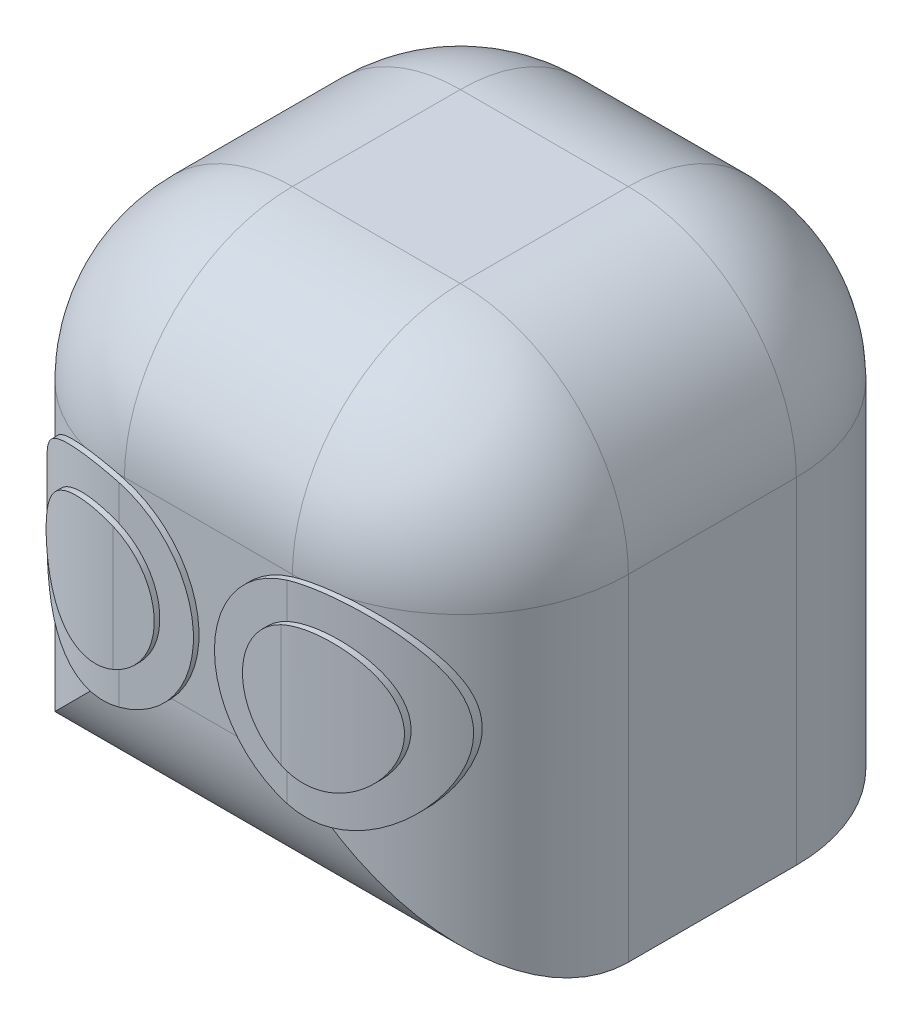
SolidWorks part; units mm, degrees
ref_plane "Alzado" through (0, 0, 0) normal (0, 0, 1) x (1, 0, 0)
ref_plane "Planta" through (0, 0, 0) normal (0, 1, 0) x (1, 0, 0)
ref_plane "Vista lateral" through (0, 0, 0) normal (1, 0, 0) x (0, 0, -1)
sketch "Croquis1" plane through (0, 0, 0) normal (0, 0, 1) x (1, 0, 0)
  line L1 (-56.7508, 42.2925) -> (33.2492, 42.2925)
  line L2 (-56.7508, 42.2925) -> (-56.7508, -47.7075)
  line L3 (-56.7508, -47.7075) -> (33.2492, -47.7075)
  line L4 (33.2492, 42.2925) -> (33.2492, -47.7075)
extrude "Saliente-Extruir1" add sketch "Croquis1" along normal blind 90
fillet "Redondeo2" radius 30 9 edges at (33.2492, 42.2925, 45) (-11.7508, 42.2925, 90) (-56.7508, 42.2925, 45) (-11.7508, 42.2925, 0) (-11.7508, -47.7075, 90) (-56.7508, -2.7075, 0) (33.2492, -2.7075, 0) (33.2492, -2.7075, 90) (-56.7508, -2.7075, 90)
sketch "Croquis2" plane through (0, 0, 90) normal (0, 0, 1) x (1, 0, 0)
  circle A0 centre (8.3242, -5.3588) radius 18
  circle A1 centre (-31.429, -5.3588) radius 18
extrude "Saliente-Extruir2" add sketch "Croquis2" along normal blind 1 and the other way blind 12
sketch "Croquis3" plane through (0, 42.2925, 0) normal (0, 1, 0) x (1, 0, 0)
  line L7 (-11.7508, -90) -> (-11.7508, -72.6432)
  line L8 (-26.7508, -91) -> (-50.1404, -91)
  line L9 (-50.1404, -91) -> (-50.1404, -80.3451)
  line L10 (3.2492, -90) -> (-26.7508, -90) construction
  line L11 (3.2492, -91) -> (26.6389, -91)
  line L12 (26.6389, -91) -> (26.6389, -80.3451)
  arc A1 (-50.1404, -80.3451) -> (-26.7508, -91) centre (-26.7508, -60) ccw
  arc A2 (26.6389, -80.3451) -> (3.2492, -91) centre (3.2492, -60) cw
extrude "Cortar-Extruir1" cut sketch "Croquis3" against normal blind 74 contours A1 L9 L8 | L12 A2 L11
sketch "Croquis4" plane through (0, 0, 91) normal (0, 0, 1) x (1, 0, 0)
  circle A0 centre (-31.429, -5.3588) radius 12
  circle A1 centre (8.3242, -5.3588) radius 12
extrude "Saliente-Extruir3" add sketch "Croquis4" against normal blind 6 and the other way blind 1
sketch "Croquis5" plane through (0, 42.2925, 0) normal (0, 1, 0) x (1, 0, 0)
  line L0 (-26.7508, -92) -> (-43.429, -92)
  line L1 (-11.7508, -90) -> (-11.7508, -77.6771)
  line L3 (-43.429, -92) -> (-48.0873, -92)
  line L4 (-48.0873, -92) -> (-48.0873, -83.8485)
  line L5 (3.2492, -90) -> (-26.7508, -90) construction
  line L6 (24.5858, -92) -> (24.5858, -83.8485)
  line L7 (19.9274, -92) -> (24.5858, -92)
  line L8 (3.2492, -92) -> (19.9274, -92)
  arc A0 (-48.0873, -83.8485) -> (-26.7508, -92) centre (-26.7508, -60) ccw
  arc A1 (24.5858, -83.8485) -> (3.2492, -92) centre (3.2492, -60) cw
extrude "Cortar-Extruir2" cut sketch "Croquis5" against normal blind 100 contours A0 L4 L3 L0 | A1 L8 L7 L6
